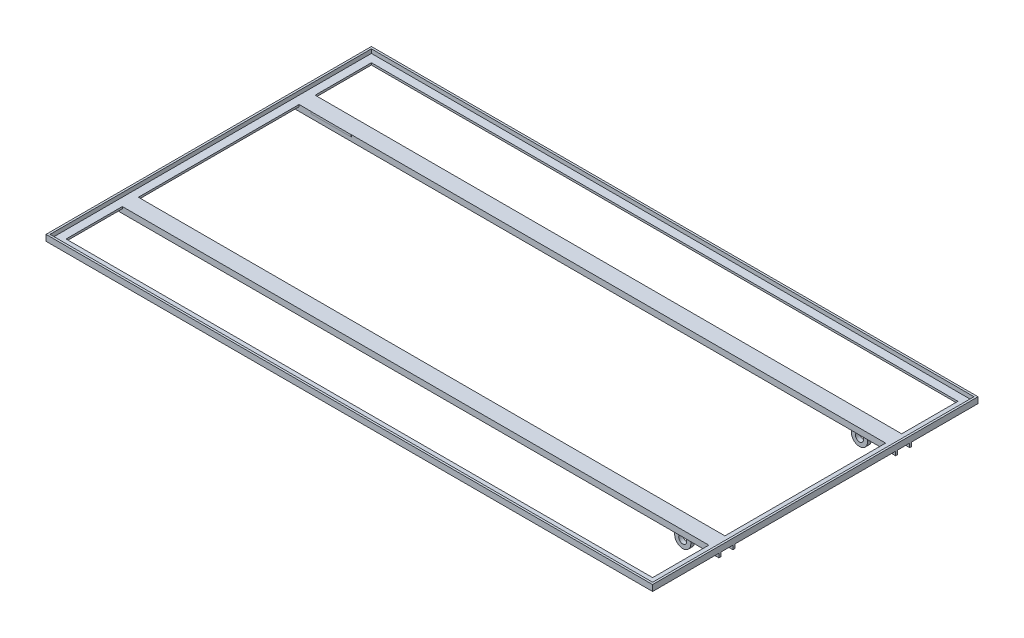
SolidWorks part; units mm, degrees
material "Plain Carbon Steel"
ref_plane "Front Plane" through (0, 0, 0) normal (0, 0, 1) x (1, 0, 0)
ref_plane "Top Plane" through (0, 0, 0) normal (0, 1, 0) x (1, 0, 0)
ref_plane "Right Plane" through (0, 0, 0) normal (1, 0, 0) x (0, 0, -1)
sketch "Sketch2" plane through (0, 0, 0) normal (0, 1, 0) x (1, 0, 0)
  line L1 (-750, 400) -> (750, 400)
  line L2 (-750, 400) -> (-750, -400)
  line L3 (-750, -400) -> (750, -400)
  line L4 (750, 400) -> (750, -400)
  line L5 (-750, 400) -> (750, -400) construction
  line L6 (-750, -400) -> (750, 400) construction
  line L7 (-755, 405) -> (755, 405)
  line L8 (-755, 405) -> (-755, -405)
  line L9 (-755, -405) -> (755, -405)
  line L10 (755, 405) -> (755, -405)
  line L11 (-755, 405) -> (755, -405) construction
  line L12 (-755, -405) -> (755, 405) construction
  point P0 (0, 0)
  point P6 (0, 0)
  dimension "D1" = 1500
  dimension "D2" = 800
  dimension "D3" = 1510
  dimension "D4" = 810
extrude "Boss-Extrude1" add sketch "Sketch2" along normal blind 10
sketch "Sketch3" plane through (0, 0, 0) normal (0, 1, 0) x (1, 0, 0)
  line L0 (-755, 405) -> (-755, -405) construction
  line L1 (755, -405) -> (-755, -405)
  line L2 (755, -405) -> (755, 405)
  line L3 (755, 405) -> (-755, 405)
  line L4 (-755, -405) -> (-755, 405)
  line L5 (755, -405) -> (-755, 405) construction
  line L6 (755, 405) -> (-755, -405) construction
  line L7 (755, 405) -> (-755, 405) construction
  line L8 (-750, 400) -> (-750, -400) construction
  line L9 (730, -380) -> (-730, -380)
  line L10 (730, -380) -> (730, -240)
  line L11 (730, 380) -> (-730, 380)
  line L12 (-730, -380) -> (-730, -240)
  line L13 (730, -380) -> (-730, 380) construction
  line L14 (730, 380) -> (-730, -380) construction
  line L15 (-750, -400) -> (750, -400) construction
  line L16 (-730, -240) -> (730, -240)
  line L17 (-730, -200) -> (-700, -200)
  line L18 (-730, 240) -> (730, 240)
  line L19 (-730, 200) -> (-700, 200)
  line L20 (-730, 240) -> (-730, 380)
  line L21 (-730, -200) -> (-730, 200)
  line L22 (730, -200) -> (730, 200)
  line L23 (730, 240) -> (730, 380)
  line L24 (0, 0) -> (-650, 0) construction
  line L25 (0, 0) -> (650, 0) construction
  line L26 (-500, 240) -> (-500, -240) construction
  line L27 (650, 240) -> (650, -240) construction
  line L28 (-600, 200) -> (600, 200)
  line L30 (-600, 200) -> (-600, -200)
  line L32 (-700, 200) -> (-700, -200)
  line L33 (-600, 200) -> (-700, -200) construction
  line L34 (-600, -200) -> (-700, 200) construction
  line L36 (600, 200) -> (600, -200)
  line L38 (700, 200) -> (700, -200)
  line L39 (600, 200) -> (700, -200) construction
  line L40 (600, -200) -> (700, 200) construction
  line L41 (-600, -200) -> (600, -200)
  line L42 (700, -200) -> (730, -200)
  line L43 (700, 200) -> (730, 200)
  point P0 (0, 0)
  point P10 (0, 0)
  dimension "D1" = 20
  dimension "D2" = 40
  dimension "20" = 20
  dimension "D3" = 40
  dimension "D4" = 200
  dimension "D5" = 200
  dimension "D6" = 650
  dimension "D7" = 650
  dimension "D8" = 100
  dimension "D9" = 100
extrude "Boss-Extrude2" add sketch "Sketch3" against normal blind 5
sketch "Sketch5" plane through (0, -5, 0) normal (0, -1, 0) x (1, 0, 0)
  line L0 (-755, 240) -> (755, 240)
  line L1 (-755, -405) -> (-755, 405) construction
  line L2 (755, 405) -> (755, -405) construction
  line L3 (755, 240) -> (755, 235)
  line L4 (755, 235) -> (-755, 235)
  line L5 (-755, 235) -> (-755, 240)
  dimension "D1" = 5
extrude "Boss-Extrude3" add sketch "Sketch5" along normal blind 10
pattern_linear "LPattern1" count 2 spacing 35 along (0, 0, -1) of "Boss-Extrude3"
pattern_linear "LPattern2" count 2 spacing 440 along (0, 0, -1) of "LPattern1", "Boss-Extrude3"
ref_plane "Plane1" through (0, 0, 220) normal (0, 0, 1) x (1, 0, 0)
sketch "Sketch6" plane through (0, 0, 220) normal (0, 0, 1) x (1, 0, 0)
  line L0 (630, -5) -> (630, -35)
  line L1 (-755, -5) -> (755, -5) construction
  line L3 (670, -35) -> (670, -5)
  line L4 (670, -5) -> (630, -5)
  line L5 (600, -5) -> (600, 0) construction
  arc A0 (670, -35) -> (630, -35) centre (650, -35) cw
  circle A1 centre (650, -35) radius 10
  dimension "D4" = 20
  dimension "D1" = 30
  dimension "D2" = 40
  dimension "30" = 30
extrude "Boss-Extrude4" add sketch "Sketch6" along normal mid plane 10
pattern_linear "LPattern3" count 2 spacing 440 along (0, 0, -1) of "Boss-Extrude4"
sketch "Sketch7" plane through (0, -5, 0) normal (0, -1, 0) x (1, 0, 0)
  line L1 (-700, 200) -> (-600, 200)
  line L2 (-700, 200) -> (-700, -199.729)
  line L3 (-700, -199.729) -> (-600, -199.729)
  line L4 (-600, 200) -> (-600, -199.729)
  line L5 (-755, 200) -> (755, 200) construction
  line L6 (700, -200) -> (600, -200)
  line L7 (700, -200) -> (700, 200)
  line L8 (700, 200) -> (600, 200)
  line L9 (600, -200) -> (600, 200)
  point P14 (-612.559, -205)
  point P17 (-600, -205)
  point P18 (600, -200)
extrude "Cut-Extrude5" cut sketch "Sketch7" against normal blind 10
